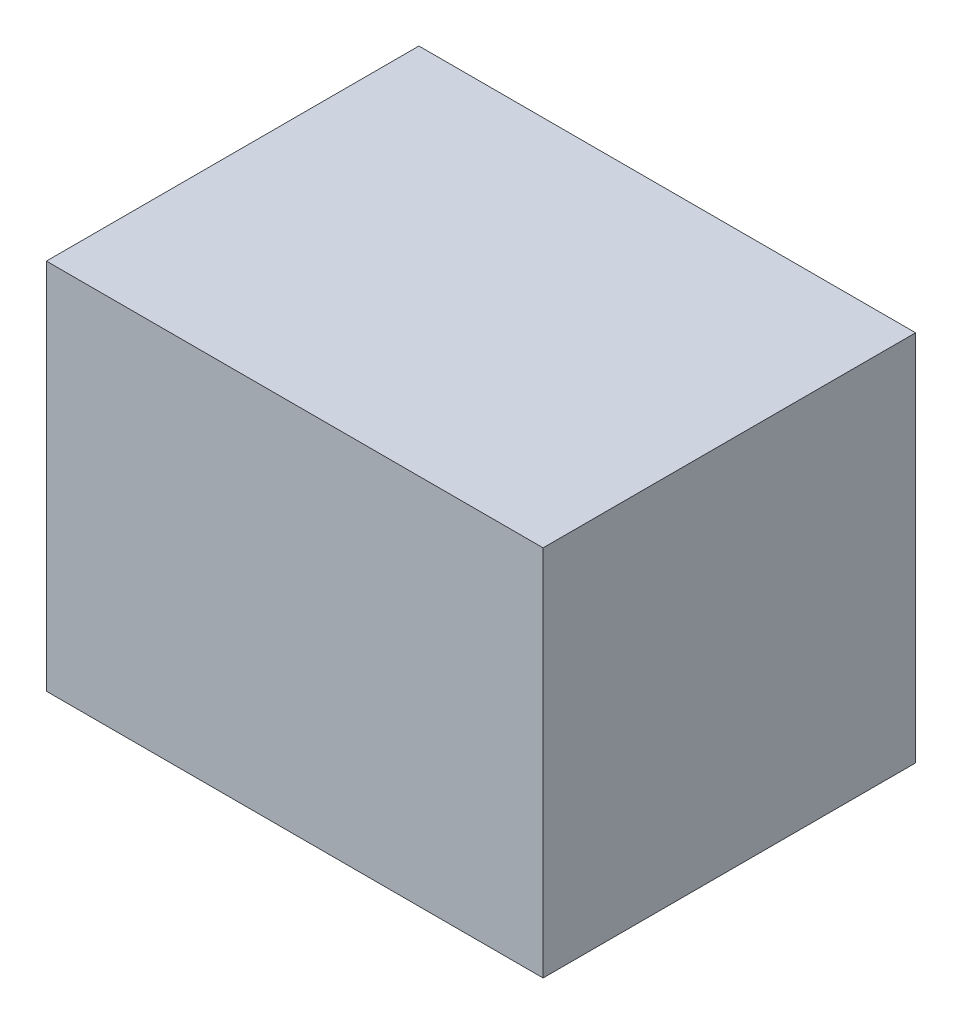
SolidWorks part; units mm, degrees
material "ABS"
ref_plane "Alzado" through (0, 0, 0) normal (0, 0, 1) x (1, 0, 0)
ref_plane "Planta" through (0, 0, 0) normal (0, 1, 0) x (1, 0, 0)
ref_plane "Vista lateral" through (0, 0, 0) normal (1, 0, 0) x (0, 0, -1)
sketch "Croquis1" plane through (0, 0, 0) normal (0, 1, 0) x (1, 0, 0)
  line L1 (-20, 15) -> (20, 15)
  line L2 (-20, 15) -> (-20, -15)
  line L3 (-20, -15) -> (20, -15)
  line L4 (20, 15) -> (20, -15)
  line L5 (-20, 15) -> (20, -15) construction
  line L6 (-20, -15) -> (20, 15) construction
  point P0 (0, 0)
  dimension "D1" = 40
  dimension "D2" = 30
extrude "Saliente-Extruir1" add sketch "Croquis1" along normal blind 30
